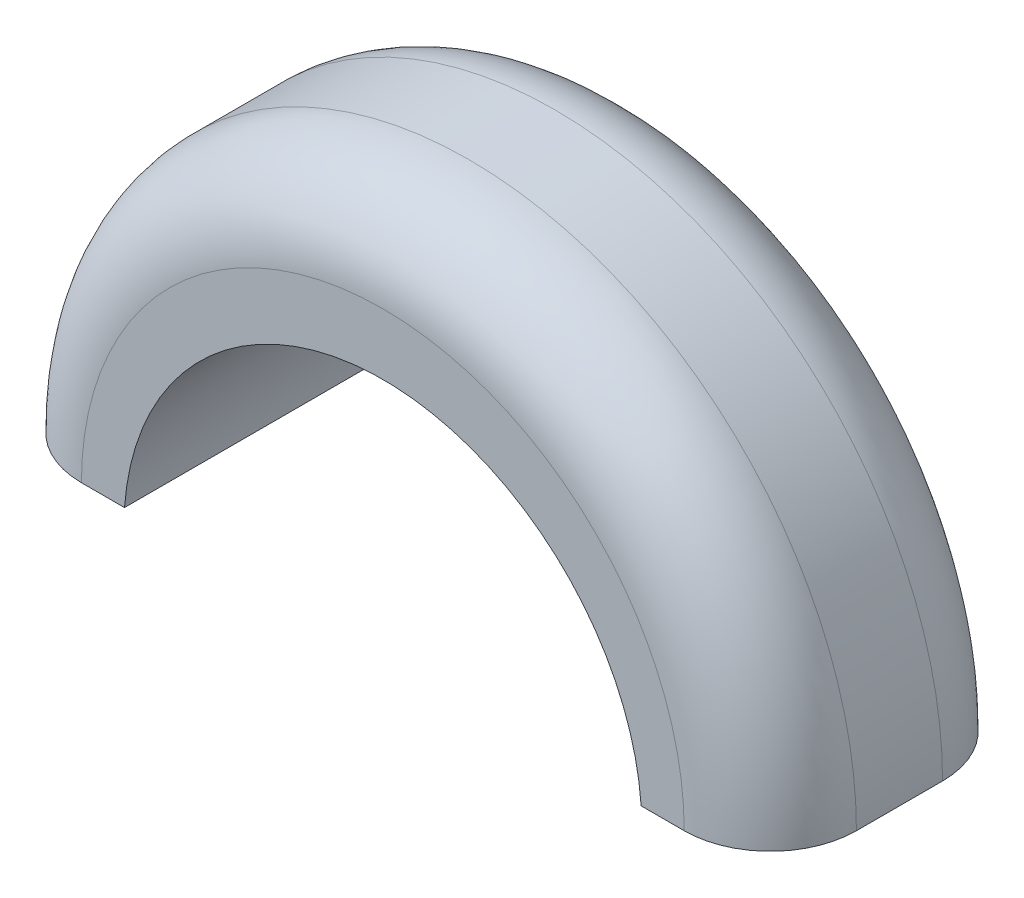
SolidWorks part; units mm, degrees
ref_plane "Front Plane" through (0, 0, 0) normal (0, 0, 1) x (1, 0, 0)
ref_plane "Top Plane" through (0, 0, 0) normal (0, 1, 0) x (1, 0, 0)
ref_plane "Right Plane" through (0, 0, 0) normal (1, 0, 0) x (0, 0, -1)
sketch "Sketch1" plane through (0, 0, 0) normal (0, 0, 1) x (1, 0, 0)
  line L1 (0, 0) -> (0.381, 0)
  line L2 (1.905, 0) -> (2.286, 0)
  arc A0 (0, 0) -> (2.286, 0) centre (1.143, 0) cw
  arc A1 (0.381, 0) -> (1.905, 0) centre (1.143, -0.0555) cw
  dimension "D1" = 2.286
  dimension "D2" = 0.381
  dimension "D3" = 0.381
extrude "Boss-Extrude1" add sketch "Sketch1" along normal blind 0.762
fillet "Fillet1" radius 0.254 2 edges at (1.143, 1.143, 0) (1.143, 1.143, 0.762)
